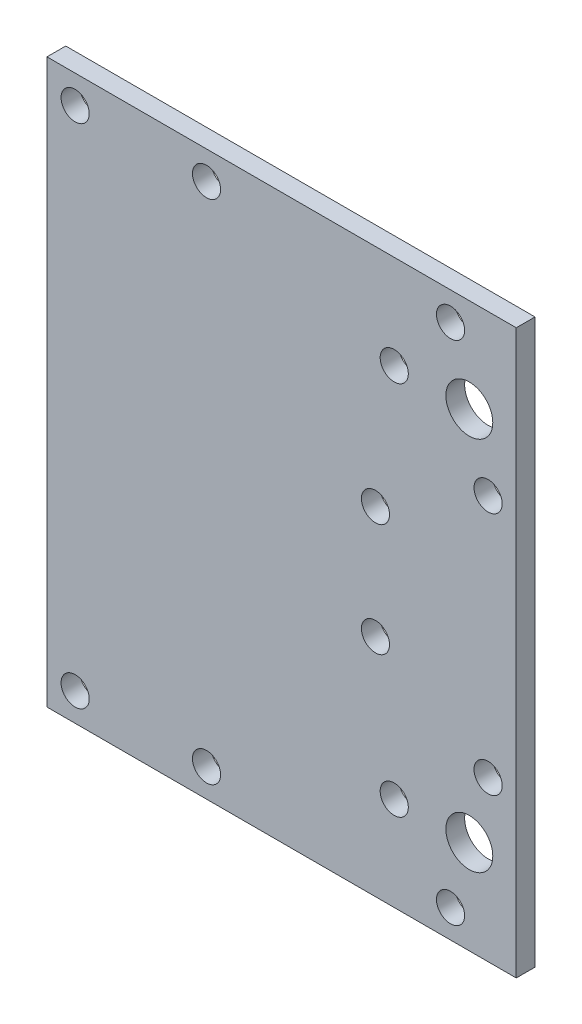
SolidWorks part; units mm, degrees
material "1060 Alloy"
ref_plane "Front Plane" through (0, 0, 0) normal (0, 0, 1) x (1, 0, 0)
ref_plane "Top Plane" through (0, 0, 0) normal (0, 1, 0) x (1, 0, 0)
ref_plane "Right Plane" through (0, 0, 0) normal (1, 0, 0) x (0, 0, -1)
sketch "Sketch1" plane through (0, 0, 0) normal (0, 0, 1) x (1, 0, 0)
  line L1 (0, 0) -> (50, 0)
  line L2 (0, 0) -> (0, 60)
  line L3 (0, 60) -> (50, 60)
  line L4 (50, 0) -> (50, 60)
  circle A0 centre (3, 57) radius 1.5
  circle A1 centre (17, 57) radius 1.5
  circle A2 centre (17, 3) radius 1.5
  circle A3 centre (3, 3) radius 1.5
  circle A4 centre (47, 17) radius 1.5
  circle A5 centre (43, 3) radius 1.5
  circle A6 centre (47, 43) radius 1.5
  circle A7 centre (43, 57) radius 1.5
  circle A8 centre (35, 24) radius 1.5
  circle A9 centre (35, 36) radius 1.5
  circle A10 centre (37, 50) radius 1.5
  circle A11 centre (37, 10) radius 1.5
  circle A12 centre (45, 50) radius 2.5
  circle A13 centre (45, 10) radius 2.5
  dimension "D1" = 35
  dimension "D14" = 3
  dimension "D16" = 3
  dimension "D18" = 13
  dimension "D19" = 5
  dimension "D22" = 5
  dimension "D2" = 12
  dimension "D3" = 3
  dimension "D4" = 14
  dimension "D5" = 3
  dimension "D6" = 4
  dimension "D7" = 3
  dimension "D8" = 3
  dimension "D9" = 14
  dimension "D10" = 14
  dimension "D11" = 60
  dimension "D12" = 3
  dimension "D13" = 3
  dimension "D15" = 24
  dimension "D17" = 50
  dimension "D20" = 10
  dimension "D21" = 10
extrude "Boss-Extrude1" add sketch "Sketch1" along normal blind 2
